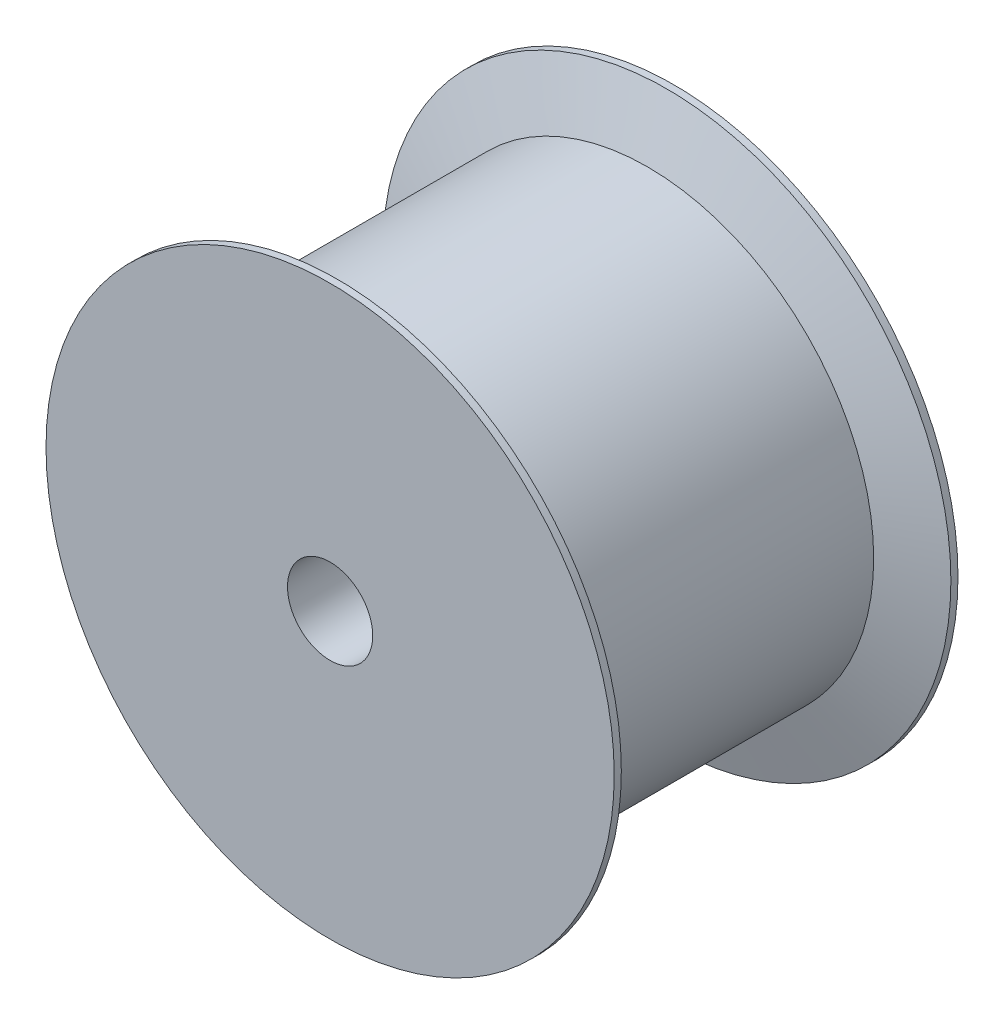
SolidWorks part; units mm, degrees
ref_plane "前基準面" through (0, 0, 0) normal (0, 0, 1) x (1, 0, 0)
ref_plane "上基準面" through (0, 0, 0) normal (0, 1, 0) x (1, 0, 0)
ref_plane "右基準面" through (0, 0, 0) normal (1, 0, 0) x (0, 0, -1)
sketch "草圖2" plane through (0, 0, 0) normal (0, 1, 0) x (1, 0, 0)
  line L0 (20, -0.5) -> (15.915, -1.85)
  line L1 (0, 0) -> (20, 0)
  line L2 (0, 0) -> (0, -24.2)
  line L3 (0, -24.2) -> (20, -24.2)
  line L4 (20, 0) -> (20, -0.5)
  line L5 (15.915, -1.85) -> (15.915, -22.35)
  line L6 (15.915, -22.35) -> (20, -23.7)
  line L7 (20, -23.7) -> (20, -24.2)
  dimension "D1" = 24.2
  dimension "D2" = 20
  dimension "D3" = 15.915
  dimension "D4" = 1.85
  dimension "D5" = 1.85
  dimension "D6" = 0.5
  dimension "D7" = 0.5
revolve "旋轉1" add sketch "草圖2" angle 360 about L2
sketch "草圖3" plane through (0, 0, 24.2) normal (0, 0, 1) x (1, 0, 0)
  circle A0 centre (0, 0) radius 3
  dimension "D1" = 6
extrude "除料-伸長1" cut sketch "草圖3" against normal through all
